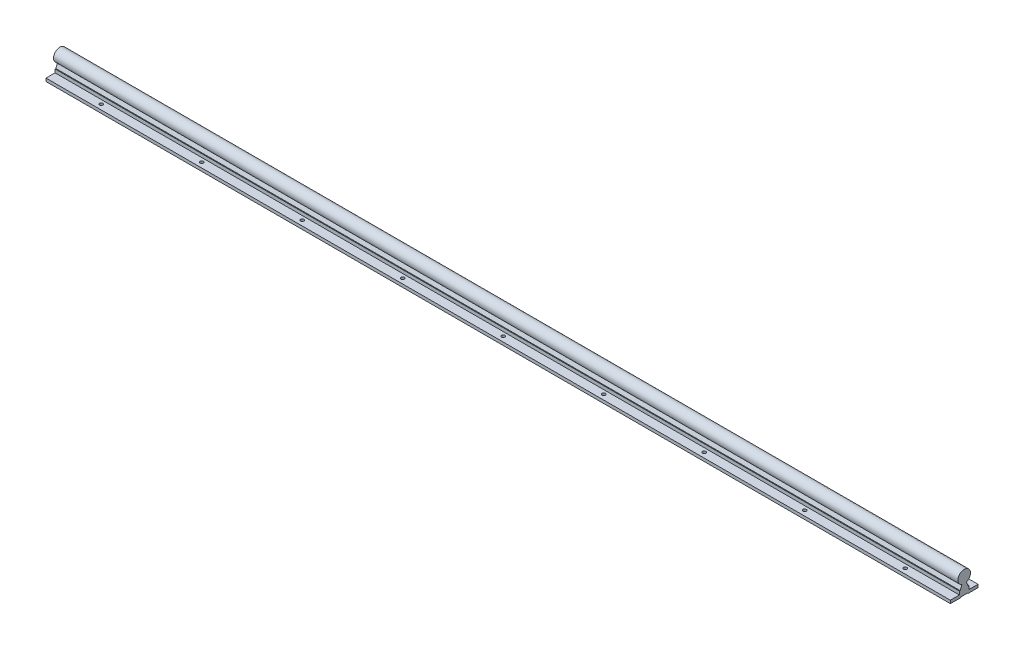
SolidWorks part; units mm, degrees
ref_plane "前视基准面" through (0, 0, 0) normal (0, 0, 1) x (1, 0, 0)
ref_plane "上视基准面" through (0, 0, 0) normal (0, 1, 0) x (1, 0, 0)
ref_plane "右视基准面" through (0, 0, 0) normal (1, 0, 0) x (0, 0, -1)
sketch "草图1" plane through (0, 0, 0) normal (1, 0, 0) x (0, 0, -1)
  line L0 (38.0237, 12.7102) -> (38.0237, 6.7102)
  line L1 (38.0237, 6.7102) -> (18.0237, 6.7102)
  line L2 (18.0237, 6.7102) -> (16.8237, 7.9102)
  line L3 (16.8237, 7.9102) -> (4.2237, 7.9102)
  line L4 (4.2237, 7.9102) -> (3.0237, 6.7102)
  line L5 (3.0237, 6.7102) -> (-16.9763, 6.7102)
  line L6 (-16.9763, 6.7102) -> (-16.9763, 12.7102)
  line L7 (-16.9763, 12.7102) -> (1.0237, 12.7102)
  line L8 (1.0237, 12.7102) -> (1.0237, 19.4102)
  line L9 (1.0237, 19.4102) -> (2.5937, 19.4102)
  line L10 (18.4537, 19.4102) -> (15.072, 28.0671)
  line L11 (38.0237, 12.7102) -> (20.0237, 12.7102)
  line L12 (20.0237, 12.7102) -> (20.0237, 19.4102)
  line L13 (20.0237, 19.4102) -> (18.4537, 19.4102)
  line L14 (2.5937, 19.4102) -> (5.9754, 28.0671)
  line L15 (10.5237, 7.9102) -> (10.5237, 59.2349) construction
  arc A0 (15.072, 28.0671) -> (5.9754, 28.0671) centre (10.5237, 39.7102) ccw
  dimension "D18" = 25
  dimension "D1" = 6
  dimension "D2" = 6
  dimension "D3" = 20
  dimension "D4" = 55
  dimension "D5" = 1.2
  dimension "D6" = 1.2
  dimension "D7" = 20
  dimension "D8" = 1.2
  dimension "D9" = 1.2
  dimension "D10" = 18
  dimension "D11" = 18
  dimension "D12" = 6.7
  dimension "D13" = 6.7
  dimension "D14" = 1.57
  dimension "D15" = 1.57
  dimension "D16" = 3.3817
  dimension "D17" = 3.3817
  dimension "D19" = 33
  dimension "D20" = 27.5
extrude "凸台-拉伸1" add sketch "草图1" along normal blind 1800
hole_wizard "Ø6.6 (6.6) 直径孔1" positions "3D草图1" profile "草图2" hole size "Ø6.6" standard "GB" end condition through all
sketch3d "3D草图1"
  line L0 (0, 12.7102, -38.0237) -> (0, 12.7102, -20.0237) construction
  line L1 (0, 12.7102, -1.0237) -> (0, 12.7102, 16.9763) construction
  line L2 (1800, 12.7102, -38.0237) -> (0, 12.7102, -38.0237) construction
  point P0 (100, 12.7102, -28.0237)
  point P2 (100, 12.7102, 6.9763)
  dimension "D1" = 100
  dimension "D2" = 100
  dimension "D3" = 35
  dimension "D4" = 10
sketch "草图2" plane through (100, 12.7102, -28.0237) normal (1, 0, 0) x (0, 0, 1)
  line L0 (0, 0) -> (0, 6)
  line L1 (0, 6) -> (3.3, 6)
  line L2 (3.3, 6) -> (3.3, 0)
  line L5 (3.3, 0) -> (0, 0)
  line L11 (0, -6.35) -> (0, 107.95) construction
  dimension "通孔孔直径" = 6.6
  dimension "通孔孔深度" = 6
pattern_linear "阵列(线性)1" count 9 spacing 200 along (1, 0, 0) of "Ø6.6 (6.6) 直径孔1"
